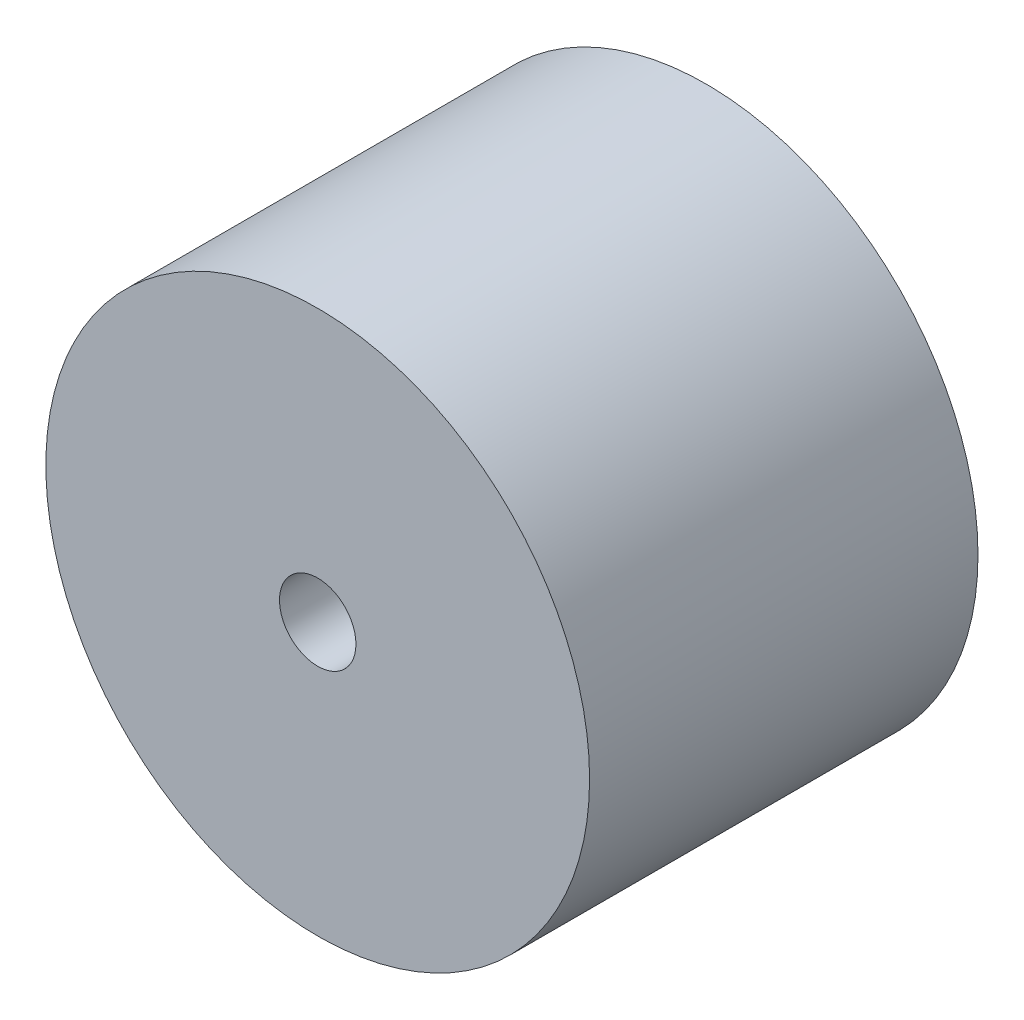
SolidWorks part; units mm, degrees
material "Silicon Rubber"
ref_plane "Front Plane" through (0, 0, 0) normal (0, 0, 1) x (1, 0, 0)
ref_plane "Top Plane" through (0, 0, 0) normal (0, 1, 0) x (1, 0, 0)
ref_plane "Right Plane" through (0, 0, 0) normal (1, 0, 0) x (0, 0, -1)
sketch "Sketch2" plane through (0, 0, 0) normal (0, 0, 1) x (1, 0, 0)
  circle A0 centre (0, 0) radius 17.78
  circle A1 centre (0, 0) radius 2.5
  dimension "D1" = 35.56
  dimension "D2" = 5
extrude "Boss-Extrude1" add sketch "Sketch2" along normal blind 25.4
